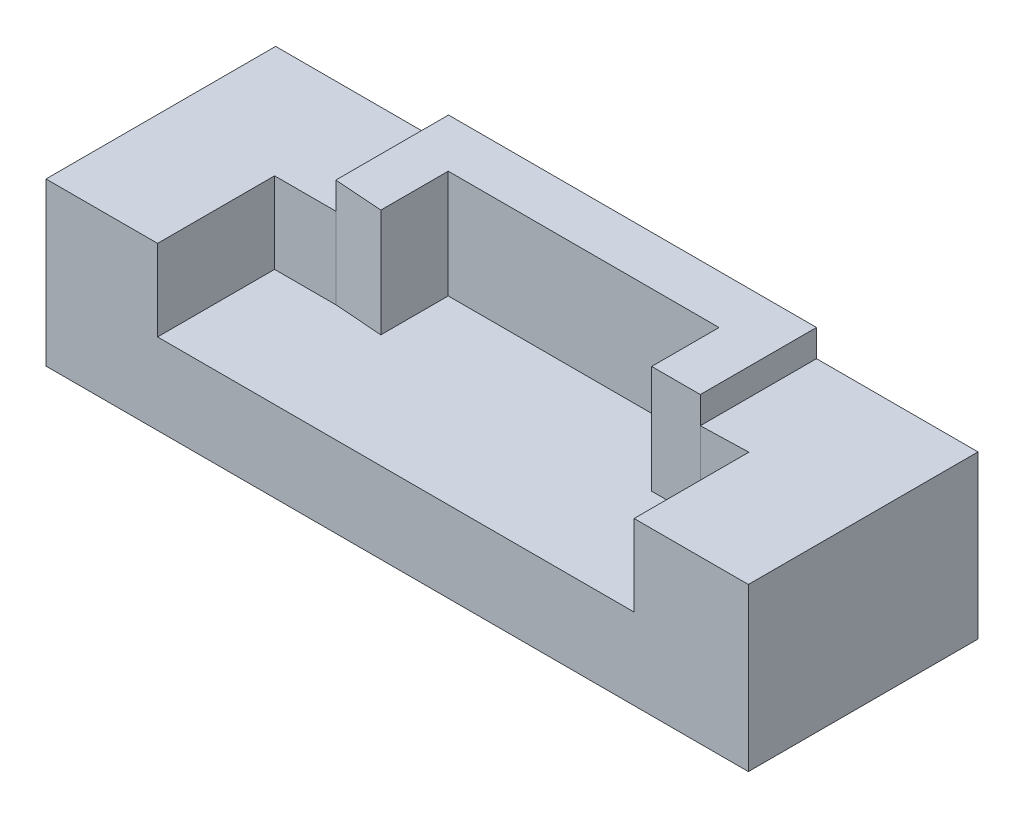
SolidWorks part; units mm, degrees
ref_plane "Front Plane" through (0, 0, 0) normal (0, 0, 1) x (1, 0, 0)
ref_plane "Top Plane" through (0, 0, 0) normal (0, 1, 0) x (1, 0, 0)
ref_plane "Right Plane" through (0, 0, 0) normal (1, 0, 0) x (0, 0, -1)
sketch "Sketch1" plane through (0, 0, 0) normal (0, 1, 0) x (1, 0, 0)
  line L1 (-39.1739, 11.7029) -> (12.8261, 11.7029)
  line L2 (-39.1739, 11.7029) -> (-39.1739, -5.2971)
  line L3 (-39.1739, -5.2971) -> (12.8261, -5.2971)
  line L4 (12.8261, 11.7029) -> (12.8261, -5.2971)
  line L5 (-39.1739, 11.7029) -> (12.8261, -5.2971) construction
  line L6 (-39.1739, -5.2971) -> (12.8261, 11.7029) construction
  point P0 (-13.1739, 3.2029)
  dimension "D1" = 17
  dimension "D2" = 52
extrude "Boss-Extrude1" add sketch "Sketch1" along normal blind 6
sketch "Sketch2" plane through (0, 6, 0) normal (0, 1, 0) x (1, 0, 0)
  line L0 (-39.1739, 11.7029) -> (-26.3739, 11.7029)
  line L1 (12.8261, 11.7029) -> (-39.1739, 11.7029) construction
  line L2 (-39.1739, 11.7029) -> (-39.1739, -5.2971)
  line L3 (-39.1739, -5.2971) -> (12.8261, -5.2971) construction
  line L4 (-39.1739, 11.7029) -> (-39.1739, -5.2971) construction
  line L5 (-39.1739, -5.2971) -> (-30.9138, -5.2971)
  line L6 (-30.9138, -5.2971) -> (-30.9138, 3.3656)
  line L7 (-30.9138, 3.3656) -> (-26.3739, 3.3656)
  line L8 (-26.3739, 3.3656) -> (-26.3739, 11.7029)
  dimension "D1" = 12.8
extrude "Boss-Extrude2" add sketch "Sketch2" along normal blind 6
sketch "Sketch3" plane through (0, 6, 0) normal (0, 1, 0) x (1, 0, 0)
  line L0 (-26.3739, 11.7029) -> (0.8702, 11.7029)
  line L1 (12.8261, 11.7029) -> (-26.3739, 11.7029) construction
  line L2 (0.8702, 11.7029) -> (0.8702, 3.1018)
  line L3 (0.8702, 3.1018) -> (-2.7332, 3.1018)
  line L4 (-2.7332, 3.1018) -> (-2.7332, 8.0911)
  line L5 (-2.7332, 8.0911) -> (-22.783, 8.0911)
  line L6 (-22.783, 8.0911) -> (-22.783, 3.1018)
  line L7 (-22.783, 3.1018) -> (-26.3739, 3.3656)
  line L8 (-26.3739, 3.3656) -> (-26.3739, 11.7029) construction
  line L9 (-26.3739, 3.3656) -> (-26.3739, 11.7029) construction
  line L10 (-26.3739, 3.3656) -> (-26.3739, 11.7029)
  line L11 (0.8702, 11.7029) -> (12.8261, 11.7029)
  line L12 (12.8261, 11.7029) -> (12.8261, -5.2971)
  line L13 (-30.9138, -5.2971) -> (12.8261, -5.2971) construction
  line L14 (12.8261, -5.2971) -> (12.8261, 11.7029) construction
  line L15 (12.8261, -5.2971) -> (4.3812, -5.2971)
  line L16 (4.3812, -5.2971) -> (4.3812, 3.1018)
  line L17 (4.3812, 3.1018) -> (0.8702, 3.1018)
  line M1 (-26.3739, 11.7029) -> (-26.3739, 3.3656)
  line M6 (12.8261, 11.7029) -> (-26.3739, 11.7029)
extrude "Boss-Extrude4" add sketch "Sketch3" along normal blind 8 contours L7 L6 L5 L4 L3 L2 M6 M1
sketch "Sketch4" plane through (0, 6, 0) normal (0, 1, 0) x (1, 0, 0)
  line L0 (0.8702, 11.7029) -> (12.8261, 11.7029)
  line L1 (12.8261, 11.7029) -> (12.8261, -5.2971)
  line L2 (12.8261, -5.2971) -> (4.3644, -5.2971)
  line L3 (-30.9138, -5.2971) -> (12.8261, -5.2971) construction
  line L4 (4.3644, -5.2971) -> (4.3644, 3.2029)
  line L5 (4.3644, 3.2029) -> (0.8702, 3.1018)
  line L6 (0.8702, 3.1018) -> (0.8702, 11.7029)
extrude "Boss-Extrude5" add sketch "Sketch4" along normal blind 6
